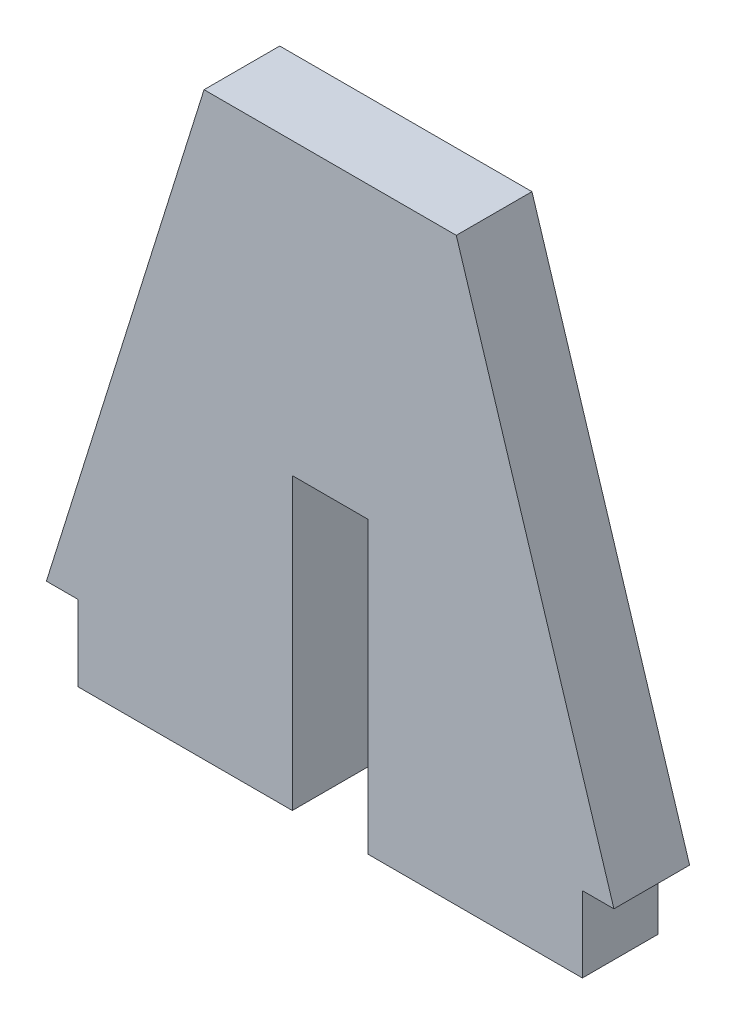
SolidWorks part; units mm, degrees
ref_plane "Front Plane" through (0, 0, 0) normal (0, 0, 1) x (1, 0, 0)
ref_plane "Top Plane" through (0, 0, 0) normal (0, 1, 0) x (1, 0, 0)
ref_plane "Right Plane" through (0, 0, 0) normal (1, 0, 0) x (0, 0, -1)
sketch "Sketch1" plane through (0, 0, 0) normal (0, 0, 1) x (1, 0, 0)
  line L0 (-20, 0) -> (20, 0)
  line L1 (20, 0) -> (20, 6)
  line L2 (-20, 6) -> (-22.5, 6)
  line L3 (10, 46) -> (-10, 46)
  line L4 (-22.5, 6) -> (-10, 46)
  line L5 (-20, 6) -> (-20, 0)
  line L6 (0, 46) -> (0, 0) construction
  line L7 (10, 46) -> (22.5, 6)
  line L8 (22.5, 6) -> (20, 6)
  dimension "D1" = 6
  dimension "D2" = 40
  dimension "D3" = 40
  dimension "D4" = 20
  dimension "D5" = 45
extrude "Boss-Extrude1" add sketch "Sketch1" along normal mid plane 6
sketch "Sketch2" plane through (0, 0, 3) normal (0, 0, 1) x (1, 0, 0)
  line L1 (-3, 0) -> (3, 0)
  line L2 (-3, 0) -> (-3, 23)
  line L3 (-3, 23) -> (3, 23)
  line L4 (3, 0) -> (3, 23)
  line L5 (0, 23) -> (0, 46) construction
  line L6 (-20, 0) -> (20, 0) construction
  line L7 (10, 46) -> (-10, 46) construction
  dimension "D1" = 6
extrude "Cut-Extrude1" cut sketch "Sketch2" against normal through all
